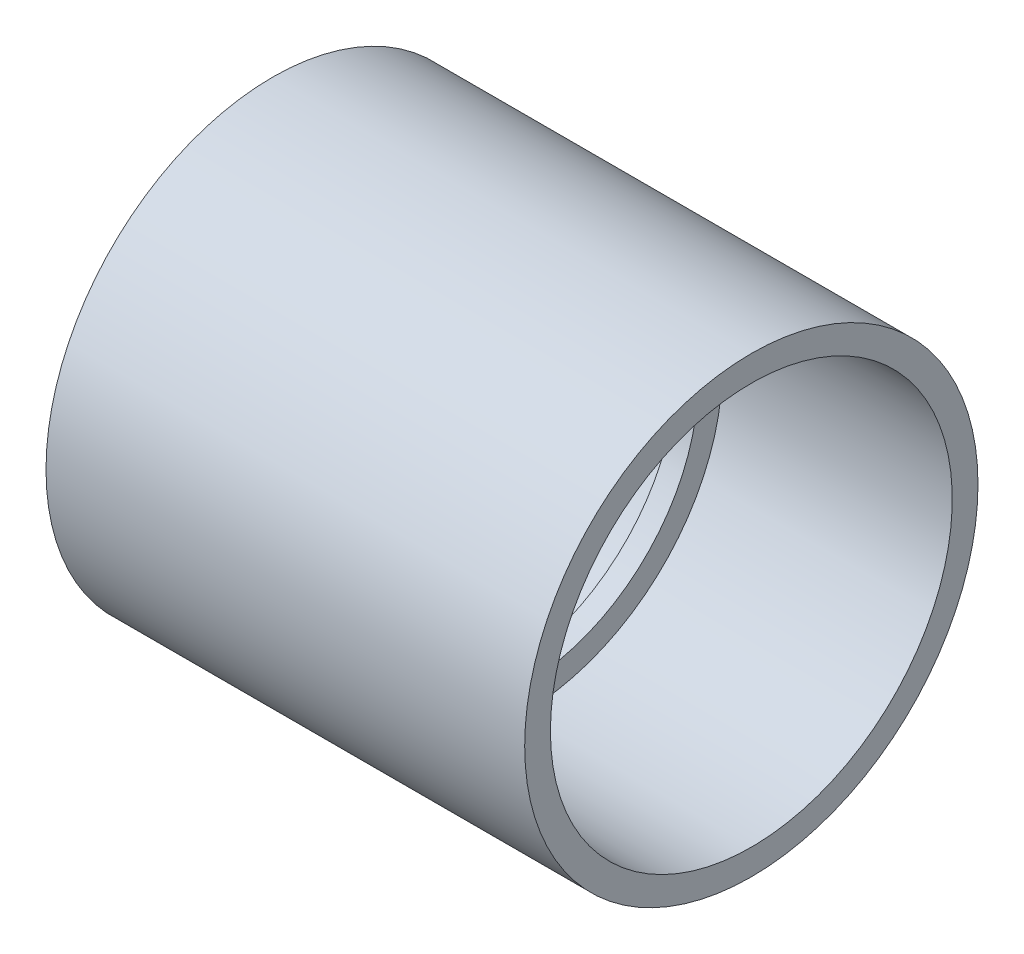
SolidWorks part; units mm, degrees
material "PVC Rigid"
ref_plane "Front Plane" through (0, 0, 0) normal (0, 0, 1) x (1, 0, 0)
ref_plane "Top Plane" through (0, 0, 0) normal (0, 1, 0) x (1, 0, 0)
ref_plane "Right Plane" through (0, 0, 0) normal (1, 0, 0) x (0, 0, -1)
sketch "Sketch0" plane through (0, 0, 0) normal (0, 0, 1) x (1, 0, 0)
  line L0 (-53.1876, 0) -> (2.3876, 0) construction
  line L2 (-2.3876, 0) -> (2.3876, 0) construction
  line L3 (-53.1876, 0) -> (53.1876, 0) construction
  line L4 (-53.1876, 50.3682) -> (-53.1876, -50.3682) construction
  line L5 (-2.3876, 44.3484) -> (-53.1876, 44.6532) construction
  line L6 (-2.3876, 44.3484) -> (-2.3876, -44.3484) construction
  line L7 (-2.3876, -44.3484) -> (-53.1876, -44.6532) construction
  line L8 (-53.1876, 44.6532) -> (-53.1876, -44.6532) construction
  line L14 (-2.3876, 38.9636) -> (-2.3876, -38.9636) construction
  dimension "N" = 4.7752
  dimension "M" = 100.7364
  dimension "OD A" = 89.3064
  dimension "OD B" = 88.6968
  dimension "ID" = 77.9272
  dimension "L" = 106.3752
sketch "Sketch1" plane through (0, 0, 0) normal (0, 0, 1) x (1, 0, 0)
  line L0 (-53.1876, 0) -> (2.3876, 0) construction
  line L1 (-53.1876, 0) -> (2.3876, 0) construction
  line L2 (-2.3876, -38.9636) -> (2.3876, -38.9636)
  line L3 (53.1876, -44.6532) -> (2.3876, -44.3484)
  line L4 (-53.1876, -50.3682) -> (-53.1876, -44.6532)
  line L5 (-53.1876, -44.6532) -> (-2.3876, -44.3484)
  line L6 (53.1876, -50.3682) -> (53.1876, -44.6532)
  line L7 (-2.3876, -44.3484) -> (-2.3876, -38.9636)
  line L8 (2.3876, -44.3484) -> (2.3876, -38.9636)
  line L9 (53.1876, -50.3682) -> (-53.1876, -50.3682)
  line L10 (0, 0) -> (0, -38.9636) construction
revolve "Revolve1" add sketch "Sketch1" angle 360 about L1
